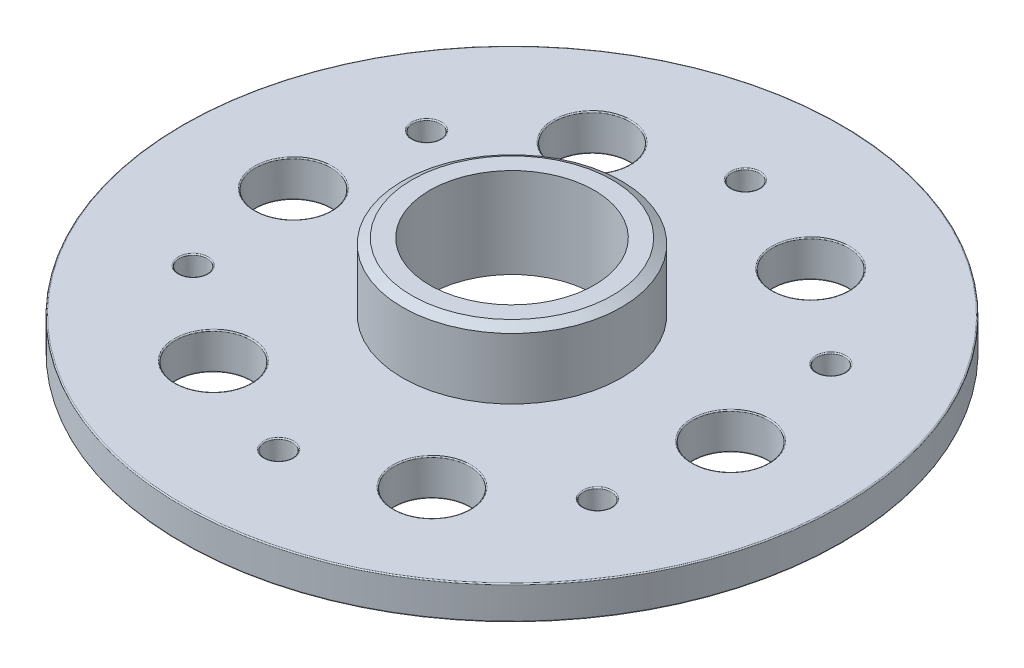
SolidWorks part; units mm, degrees
ref_plane "Спереди" through (0, 0, 0) normal (0, 0, 1) x (1, 0, 0)
ref_plane "Сверху" through (0, 0, 0) normal (0, 1, 0) x (1, 0, 0)
ref_plane "Справа" through (0, 0, 0) normal (1, 0, 0) x (0, 0, -1)
sketch "Эскиз1" plane through (0, 0, 0) normal (0, 0, 1) x (1, 0, 0)
  line L0 (0, 73.8642) -> (0, -69.8894) construction
  line L1 (-9.85, 14) -> (-9.85, 19.5)
  line L2 (-7.4, 20) -> (-9.0182, 20)
  line L3 (-9, 10.7) -> (-24.5, 10.7)
  line L4 (-9.85, 14) -> (-29.65, 14)
  line L5 (-29.65, 14) -> (-29.65, 11)
  line L6 (-9, 10.7) -> (-9, 11.9)
  line L7 (-7.4, 20) -> (-7.4, 11.9)
  line L8 (-7.4, 11.9) -> (-9, 11.9)
  line L9 (-9.0182, 20) -> (-9.85, 19.5)
  line L10 (-24.5, 23.6179) -> (-24.5, 1.2455) construction
  line L11 (-29.65, 11) -> (-24.5, 10.7)
  dimension "D1" = 7.4
  dimension "D2" = 5.5
  dimension "D3" = 0.8318
  dimension "D4" = 29.65
  dimension "D5" = 3.3
  dimension "D6" = 20
  dimension "D7" = 9
  dimension "D8" = 1.2
  dimension "D9" = 1.6182
  dimension "D10" = 0.5
  dimension "D11" = 24.5
  dimension "D12" = 3
revolve "Повернуть1" add sketch "Эскиз1" angle 360 about L0
sketch "Эскиз3" plane through (0, 10.7, 0) normal (0, -1, 0) x (1, 0, 0)
  circle A0 centre (0, 0) radius 15
  dimension "D1" = 30
extrude "Вырез-Вытянуть2" cut sketch "Эскиз3" against normal blind 0.2
sketch "Эскиз4" plane through (0, 10.7, 0) normal (0, -1, 0) x (1, 0, 0)
  circle A0 centre (0, 21) radius 1.25
  circle A1 centre (18.1865, 10.5) radius 1.25
  circle A2 centre (18.1865, -10.5) radius 1.25
  circle A3 centre (0, -21) radius 1.25
  circle A4 centre (-18.1865, -10.5) radius 1.25
  circle A5 centre (-18.1865, 10.5) radius 1.25
  circle A6 centre (19.6675, 0) radius 3.4
  circle A7 centre (9.8338, -17.0326) radius 3.4
  circle A8 centre (-9.8338, -17.0326) radius 3.4
  circle A9 centre (-19.6675, 0) radius 3.4
  circle A10 centre (-9.8338, 17.0326) radius 3.4
  circle A11 centre (9.8338, 17.0326) radius 3.4
  point P16 (0, 0)
  point P29 (0, 0)
  dimension "D1" = 2.5
  dimension "D4" = 6.8
  dimension "D2" = 21
  dimension "D3" = 6
  dimension "D5" = 19.6675
  dimension "D6" = 6
extrude "Вырез-Вытянуть3" cut sketch "Эскиз4" against normal through all
fillet "Скругление3" radius 0.1 26 edges at (13.2338, 10.7, -17.0326) (1.25, 10.7, -21) (-6.4338, 10.7, -17.0326) (-16.9365, 10.7, -10.5) (-16.2675, 10.7, 0) (-16.9365, 10.7, 10.5) (-6.4338, 10.7, 17.0326) (1.25, 10.7, 21) (13.2338, 10.7, 17.0326) (19.4365, 10.7, 10.5) (23.0675, 10.7, 0) (19.4365, 10.7, -10.5) (-29.65, 11, 0) (16.9365, 14, 10.5) (16.2675, 14, 0) (16.9365, 14, -10.5) (6.4338, 14, -17.0326) (-1.25, 14, -21) (-13.2338, 14, -17.0326) (-19.4365, 14, -10.5) (-23.0675, 14, 0) (-19.4365, 14, 10.5) (-29.65, 14, 0) (-13.2338, 14, 17.0326) (-1.25, 14, 21) (6.4338, 14, 17.0326)
